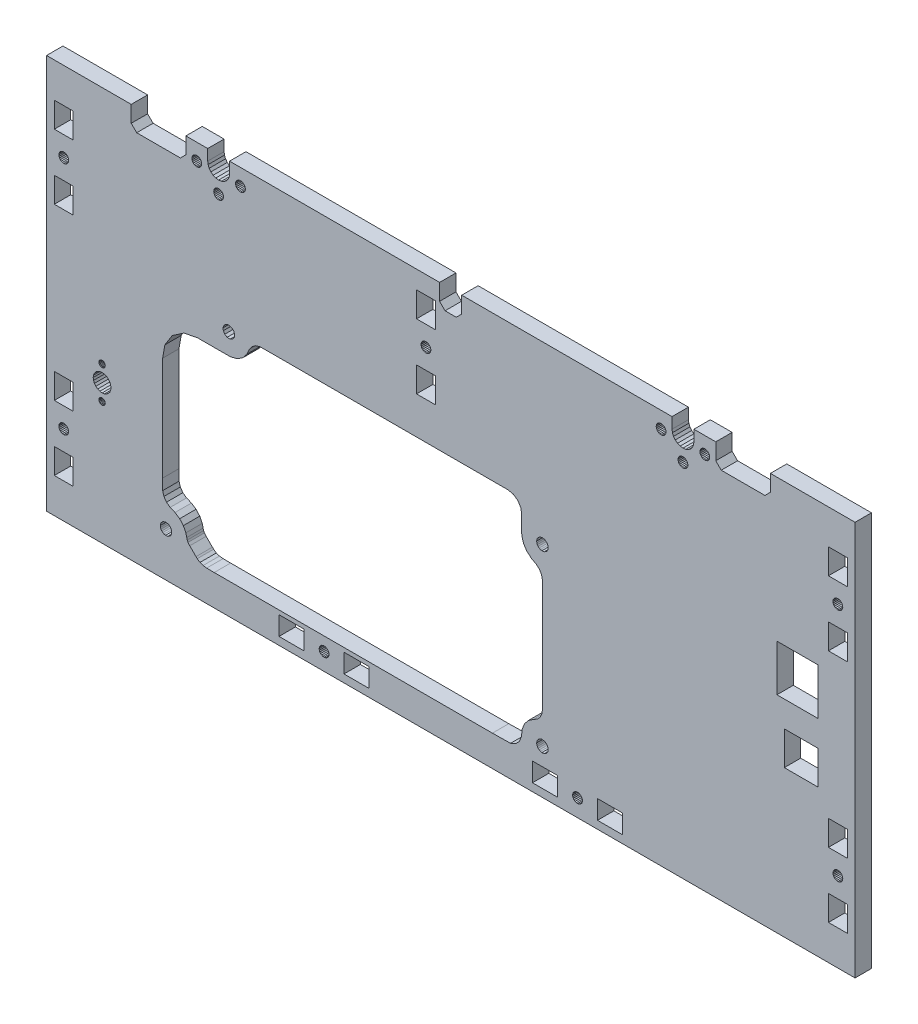
SolidWorks part; units mm, degrees
material "Maple"
ref_plane "Front Plane" through (0, 0, 0) normal (0, 0, 1) x (1, 0, 0)
ref_plane "Top Plane" through (0, 0, 0) normal (0, 1, 0) x (1, 0, 0)
ref_plane "Right Plane" through (0, 0, 0) normal (1, 0, 0) x (0, 0, -1)
sketch "Sketch1" plane through (0, 0, 0) normal (0, 0, 1) x (1, 0, 0)
  line L4690 (-23.9448, -85.7322) -> (-22.9801, -86.1318)
  line L4691 (-201.5036, -85.1681) -> (-201.2176, -85.5408)
  line L4692 (-203.9448, -78.2681) -> (-195.9448, -78.2681)
  line L4693 (-203.9448, -84.2681) -> (-203.9448, -78.2681)
  line L4694 (-187.9448, -78.2681) -> (-111.0448, -78.2681)
  line L4695 (-18.0811, -83.3033) -> (-17.9448, -82.2681)
  line L4696 (-192.98, -86.1318) -> (-191.9448, -86.2681)
  line L4697 (-187.9448, -82.2681) -> (-187.9448, -78.2681)
  line L4698 (10.0552, -78.2681) -> (41.0552, -78.2681)
  line L4699 (8.0552, -86.2681) -> (-7.9448, -86.2681)
  line L4700 (-9.9448, -78.2681) -> (-9.9448, -84.2681)
  line L4701 (-191.9448, -86.2681) -> (-190.9095, -86.1318)
  line L4702 (-25.8085, -83.3033) -> (-25.4089, -84.2681)
  line L4703 (-188.4807, -84.2681) -> (-188.0811, -83.3033)
  line L4704 (-199.0448, -82.7092) -> (-199.4789, -82.5294)
  line L4705 (10.0552, -78.2681) -> (10.0552, -84.2681)
  line L4706 (-200.8448, -85.8269) -> (-200.4106, -86.0067)
  line L4707 (-200.4106, -86.0067) -> (-199.9448, -86.0681)
  line L4708 (-200.4106, -82.5294) -> (-200.8448, -82.7092)
  line L4709 (-198.2061, -83.8022) -> (-198.3859, -83.3681)
  line L4710 (-201.6834, -83.8022) -> (-201.7448, -84.2681)
  line L4711 (41.0552, -78.2681) -> (41.0552, -222.768)
  line L4712 (-201.2176, -82.9953) -> (-201.5036, -83.3681)
  line L4713 (-198.672, -82.9953) -> (-199.0448, -82.7092)
  line L4714 (-199.9448, -82.4681) -> (-200.4106, -82.5294)
  line L4715 (-199.0448, -85.8269) -> (-198.672, -85.5408)
  line L4716 (-198.2061, -84.7339) -> (-198.1448, -84.2681)
  line L4717 (-198.1448, -84.2681) -> (-198.2061, -83.8022)
  line L4718 (-17.9448, -82.2681) -> (-17.9448, -78.2681)
  line L4719 (-198.3859, -83.3681) -> (-198.672, -82.9953)
  line L4720 (-201.5036, -83.3681) -> (-201.6834, -83.8022)
  line L4721 (-25.9448, -82.2681) -> (-25.9448, -78.2681)
  line L4722 (-20.9095, -86.1318) -> (-19.9448, -85.7322)
  line L4723 (-198.672, -85.5408) -> (-198.3859, -85.1681)
  line L4724 (-201.7448, -84.2681) -> (-201.6834, -84.7339)
  line L4725 (-19.1164, -85.0965) -> (-18.4807, -84.2681)
  line L4726 (-198.3859, -85.1681) -> (-198.2061, -84.7339)
  line L4727 (-17.9448, -78.2681) -> (-9.9448, -78.2681)
  line L4728 (-201.2176, -85.5408) -> (-200.8448, -85.8269)
  line L4729 (-189.9448, -85.7322) -> (-189.1163, -85.0965)
  line L4730 (-21.9448, -86.2681) -> (-20.9095, -86.1318)
  line L4731 (-205.9448, -86.2681) -> (-221.9448, -86.2681)
  line L4732 (-203.9448, -84.2681) -> (-205.9448, -86.2681)
  line L4733 (-200.8448, -82.7092) -> (-201.2176, -82.9953)
  line L4734 (-18.4807, -84.2681) -> (-18.0811, -83.3033)
  line L4735 (-19.9448, -85.7322) -> (-19.1164, -85.0965)
  line L4736 (-254.9447, -222.768) -> (-254.9447, -78.2681)
  line L4737 (-22.9801, -86.1318) -> (-21.9448, -86.2681)
  line L4738 (-190.9095, -86.1318) -> (-189.9448, -85.7322)
  line L4739 (-195.4089, -84.2681) -> (-194.7732, -85.0965)
  line L4740 (-254.9447, -78.2681) -> (-223.9448, -78.2681)
  line L4741 (-194.7732, -85.0965) -> (-193.9448, -85.7322)
  line L4742 (-193.9448, -85.7322) -> (-192.98, -86.1318)
  line L4743 (-24.7732, -85.0965) -> (-23.9448, -85.7322)
  line L4744 (41.0552, -222.768) -> (-254.9447, -222.768)
  line L4745 (-25.4089, -84.2681) -> (-24.7732, -85.0965)
  line L4746 (-195.9448, -82.2681) -> (-195.9448, -78.2681)
  line L4747 (-195.8085, -83.3033) -> (-195.4089, -84.2681)
  line L4748 (-188.0811, -83.3033) -> (-187.9448, -82.2681)
  line L4749 (-195.9448, -82.2681) -> (-195.8085, -83.3033)
  line L4750 (-223.9448, -84.2681) -> (-223.9448, -78.2681)
  line L4751 (-223.9448, -84.2681) -> (-221.9448, -86.2681)
  line L4752 (-25.9448, -82.2681) -> (-25.8085, -83.3033)
  line L4753 (-199.4789, -82.5294) -> (-199.9448, -82.4681)
  line L4754 (-189.1163, -85.0965) -> (-188.4807, -84.2681)
  line L4755 (-201.6834, -84.7339) -> (-201.5036, -85.1681)
  line L4756 (10.0552, -84.2681) -> (8.0552, -86.2681)
  line L4757 (-9.9448, -84.2681) -> (-7.9448, -86.2681)
  line L4758 (-199.9448, -86.0681) -> (-199.4789, -86.0067)
  line L4759 (-199.4789, -86.0067) -> (-199.0448, -85.8269)
  line L4760 (35.2215, -105.6777) -> (34.7552, -105.6163)
  line L4761 (35.656, -105.8577) -> (35.2215, -105.6777)
  line L4762 (36.0292, -106.144) -> (35.656, -105.8577)
  line L4763 (36.3155, -106.5172) -> (36.0292, -106.144)
  line L4764 (36.4955, -106.9517) -> (36.3155, -106.5172)
  line L4765 (36.5569, -107.418) -> (36.4955, -106.9517)
  line L4766 (36.4955, -107.8844) -> (36.5569, -107.418)
  line L4767 (36.3155, -108.3189) -> (36.4955, -107.8844)
  line L4768 (36.0292, -108.6921) -> (36.3155, -108.3189)
  line L4769 (35.656, -108.9784) -> (36.0292, -108.6921)
  line L4770 (35.2215, -109.1584) -> (35.656, -108.9784)
  line L4771 (34.7552, -109.2198) -> (35.2215, -109.1584)
  line L4772 (34.2888, -109.1584) -> (34.7552, -109.2198)
  line L4773 (33.8543, -108.9784) -> (34.2888, -109.1584)
  line L4774 (33.4811, -108.6921) -> (33.8543, -108.9784)
  line L4775 (33.1948, -108.3189) -> (33.4811, -108.6921)
  line L4776 (33.0148, -107.8844) -> (33.1948, -108.3189)
  line L4777 (32.9534, -107.418) -> (33.0148, -107.8844)
  line L4778 (33.0148, -106.9517) -> (32.9534, -107.418)
  line L4779 (33.1948, -106.5172) -> (33.0148, -106.9517)
  line L4780 (33.4811, -106.144) -> (33.1948, -106.5172)
  line L4781 (33.8543, -105.8577) -> (33.4811, -106.144)
  line L4782 (34.2888, -105.6777) -> (33.8543, -105.8577)
  line L4783 (34.7552, -105.6163) -> (34.2888, -105.6777)
  line L4784 (-185.5047, -85.1681) -> (-185.2187, -85.5408)
  line L4785 (-185.6846, -84.7339) -> (-185.5047, -85.1681)
  line L4786 (-185.7459, -84.2681) -> (-185.6846, -84.7339)
  line L4787 (-185.6846, -83.8022) -> (-185.7459, -84.2681)
  line L4788 (-185.5047, -83.3681) -> (-185.6846, -83.8022)
  line L4789 (-185.2187, -82.9953) -> (-185.5047, -83.3681)
  line L4790 (-184.8459, -82.7092) -> (-185.2187, -82.9953)
  line L4791 (-184.4118, -82.5294) -> (-184.8459, -82.7092)
  line L4792 (-183.9459, -82.4681) -> (-184.4118, -82.5294)
  line L4793 (-183.48, -82.5294) -> (-183.9459, -82.4681)
  line L4794 (-183.0459, -82.7092) -> (-183.48, -82.5294)
  line L4795 (-182.6731, -82.9953) -> (-183.0459, -82.7092)
  line L4796 (-182.387, -83.3681) -> (-182.6731, -82.9953)
  line L4797 (-182.2072, -83.8022) -> (-182.387, -83.3681)
  line L4798 (-182.1459, -84.2681) -> (-182.2072, -83.8022)
  line L4799 (-182.2072, -84.7339) -> (-182.1459, -84.2681)
  line L4800 (-182.387, -85.1681) -> (-182.2072, -84.7339)
  line L4801 (-182.6731, -85.5408) -> (-182.387, -85.1681)
  line L4802 (-183.0459, -85.8269) -> (-182.6731, -85.5408)
  line L4803 (-183.48, -86.0067) -> (-183.0459, -85.8269)
  line L4804 (-183.9459, -86.0681) -> (-183.48, -86.0067)
  line L4805 (-184.4118, -86.0067) -> (-183.9459, -86.0681)
  line L4806 (-184.8459, -85.8269) -> (-184.4118, -86.0067)
  line L4807 (-185.2187, -85.5408) -> (-184.8459, -85.8269)
  line L4808 (-21.0448, -92.3269) -> (-20.672, -92.0408)
  line L4809 (-21.4789, -92.5067) -> (-21.0448, -92.3269)
  line L4810 (-21.9448, -92.5681) -> (-21.4789, -92.5067)
  line L4811 (-22.4107, -92.5067) -> (-21.9448, -92.5681)
  line L4812 (-22.8448, -92.3269) -> (-22.4107, -92.5067)
  line L4813 (-23.2176, -92.0408) -> (-22.8448, -92.3269)
  line L4814 (-23.5037, -91.6681) -> (-23.2176, -92.0408)
  line L4815 (-23.6835, -91.2339) -> (-23.5037, -91.6681)
  line L4816 (-23.7448, -90.7681) -> (-23.6835, -91.2339)
  line L4817 (-23.6835, -90.3022) -> (-23.7448, -90.7681)
  line L4818 (-23.5037, -89.8681) -> (-23.6835, -90.3022)
  line L4819 (-23.2176, -89.4953) -> (-23.5037, -89.8681)
  line L4820 (-22.8448, -89.2092) -> (-23.2176, -89.4953)
  line L4821 (-22.4107, -89.0294) -> (-22.8448, -89.2092)
  line L4822 (-21.9448, -88.9681) -> (-22.4107, -89.0294)
  line L4823 (-21.4789, -89.0294) -> (-21.9448, -88.9681)
  line L4824 (-21.0448, -89.2092) -> (-21.4789, -89.0294)
  line L4825 (-20.672, -89.4953) -> (-21.0448, -89.2092)
  line L4826 (-20.386, -89.8681) -> (-20.672, -89.4953)
  line L4827 (-20.2062, -90.3022) -> (-20.386, -89.8681)
  line L4828 (-20.1448, -90.7681) -> (-20.2062, -90.3022)
  line L4829 (-20.2062, -91.2339) -> (-20.1448, -90.7681)
  line L4830 (-20.386, -91.6681) -> (-20.2062, -91.2339)
  line L4831 (-20.672, -92.0408) -> (-20.386, -91.6681)
  line L4832 (-15.6846, -83.8022) -> (-15.7459, -84.2681)
  line L4833 (-15.5048, -83.3681) -> (-15.6846, -83.8022)
  line L4834 (-15.2187, -82.9953) -> (-15.5048, -83.3681)
  line L4835 (-14.8459, -82.7092) -> (-15.2187, -82.9953)
  line L4836 (-14.4118, -82.5294) -> (-14.8459, -82.7092)
  line L4837 (-13.9459, -82.4681) -> (-14.4118, -82.5294)
  line L4838 (-13.4801, -82.5294) -> (-13.9459, -82.4681)
  line L4839 (-13.0459, -82.7092) -> (-13.4801, -82.5294)
  line L4840 (-12.6731, -82.9953) -> (-13.0459, -82.7092)
  line L4841 (-12.3871, -83.3681) -> (-12.6731, -82.9953)
  line L4842 (-12.2073, -83.8022) -> (-12.3871, -83.3681)
  line L4843 (-12.1459, -84.2681) -> (-12.2073, -83.8022)
  line L4844 (-12.2073, -84.7339) -> (-12.1459, -84.2681)
  line L4845 (-12.3871, -85.1681) -> (-12.2073, -84.7339)
  line L4846 (-12.6731, -85.5408) -> (-12.3871, -85.1681)
  line L4847 (-13.0459, -85.8269) -> (-12.6731, -85.5408)
  line L4848 (-13.4801, -86.0067) -> (-13.0459, -85.8269)
  line L4849 (-13.9459, -86.0681) -> (-13.4801, -86.0067)
  line L4850 (-14.4118, -86.0067) -> (-13.9459, -86.0681)
  line L4851 (-14.8459, -85.8269) -> (-14.4118, -86.0067)
  line L4852 (-15.2187, -85.5408) -> (-14.8459, -85.8269)
  line L4853 (-15.5048, -85.1681) -> (-15.2187, -85.5408)
  line L4854 (-15.6846, -84.7339) -> (-15.5048, -85.1681)
  line L4855 (-15.7459, -84.2681) -> (-15.6846, -84.7339)
  line L4856 (-250.2051, -108.4189) -> (-249.9188, -108.7921)
  line L4857 (-250.3851, -107.9844) -> (-250.2051, -108.4189)
  line L4858 (-250.4465, -107.518) -> (-250.3851, -107.9844)
  line L4859 (-250.3851, -107.0517) -> (-250.4465, -107.518)
  line L4860 (-250.2051, -106.6172) -> (-250.3851, -107.0517)
  line L4861 (-249.9188, -106.244) -> (-250.2051, -106.6172)
  line L4862 (-249.5456, -105.9577) -> (-249.9188, -106.244)
  line L4863 (-249.1111, -105.7777) -> (-249.5456, -105.9577)
  line L4864 (-248.6447, -105.7163) -> (-249.1111, -105.7777)
  line L4865 (-248.1784, -105.7777) -> (-248.6447, -105.7163)
  line L4866 (-247.7439, -105.9577) -> (-248.1784, -105.7777)
  line L4867 (-247.3707, -106.244) -> (-247.7439, -105.9577)
  line L4868 (-247.0844, -106.6172) -> (-247.3707, -106.244)
  line L4869 (-246.9044, -107.0517) -> (-247.0844, -106.6172)
  line L4870 (-246.843, -107.518) -> (-246.9044, -107.0517)
  line L4871 (-246.9044, -107.9844) -> (-246.843, -107.518)
  line L4872 (-247.0844, -108.4189) -> (-246.9044, -107.9844)
  line L4873 (-247.3707, -108.7921) -> (-247.0844, -108.4189)
  line L4874 (-247.7439, -109.0784) -> (-247.3707, -108.7921)
  line L4875 (-248.1784, -109.2584) -> (-247.7439, -109.0784)
  line L4876 (-248.6447, -109.3198) -> (-248.1784, -109.2584)
  line L4877 (-249.1111, -109.2584) -> (-248.6447, -109.3198)
  line L4878 (-249.5456, -109.0784) -> (-249.1111, -109.2584)
  line L4879 (-249.9188, -108.7921) -> (-249.5456, -109.0784)
  line L4880 (-192.8448, -92.3269) -> (-192.4106, -92.5067)
  line L4881 (-193.2176, -92.0408) -> (-192.8448, -92.3269)
  line L4882 (-193.5036, -91.6681) -> (-193.2176, -92.0408)
  line L4883 (-193.6834, -91.2339) -> (-193.5036, -91.6681)
  line L4884 (-193.7448, -90.7681) -> (-193.6834, -91.2339)
  line L4885 (-193.6834, -90.3022) -> (-193.7448, -90.7681)
  line L4886 (-193.5036, -89.8681) -> (-193.6834, -90.3022)
  line L4887 (-193.2176, -89.4953) -> (-193.5036, -89.8681)
  line L4888 (-192.8448, -89.2092) -> (-193.2176, -89.4953)
  line L4889 (-192.4106, -89.0294) -> (-192.8448, -89.2092)
  line L4890 (-191.9448, -88.9681) -> (-192.4106, -89.0294)
  line L4891 (-191.4789, -89.0294) -> (-191.9448, -88.9681)
  line L4892 (-191.0448, -89.2092) -> (-191.4789, -89.0294)
  line L4893 (-190.672, -89.4953) -> (-191.0448, -89.2092)
  line L4894 (-190.3859, -89.8681) -> (-190.672, -89.4953)
  line L4895 (-190.2061, -90.3022) -> (-190.3859, -89.8681)
  line L4896 (-190.1448, -90.7681) -> (-190.2061, -90.3022)
  line L4897 (-190.2061, -91.2339) -> (-190.1448, -90.7681)
  line L4898 (-190.3859, -91.6681) -> (-190.2061, -91.2339)
  line L4899 (-190.672, -92.0408) -> (-190.3859, -91.6681)
  line L4900 (-191.0448, -92.3269) -> (-190.672, -92.0408)
  line L4901 (-191.4789, -92.5067) -> (-191.0448, -92.3269)
  line L4902 (-191.9448, -92.5681) -> (-191.4789, -92.5067)
  line L4903 (-192.4106, -92.5067) -> (-191.9448, -92.5681)
  line L4904 (-60.5448, -218.2698) -> (-60.0785, -218.2084)
  line L4905 (-61.0111, -218.2084) -> (-60.5448, -218.2698)
  line L4906 (-61.4457, -218.0284) -> (-61.0111, -218.2084)
  line L4907 (-61.8188, -217.7421) -> (-61.4457, -218.0284)
  line L4908 (-62.1052, -217.3689) -> (-61.8188, -217.7421)
  line L4909 (-62.2851, -216.9344) -> (-62.1052, -217.3689)
  line L4910 (-62.3465, -216.468) -> (-62.2851, -216.9344)
  line L4911 (-62.2851, -216.0017) -> (-62.3465, -216.468)
  line L4912 (-62.1052, -215.5672) -> (-62.2851, -216.0017)
  line L4913 (-61.8188, -215.194) -> (-62.1052, -215.5672)
  line L4914 (-61.4457, -214.9077) -> (-61.8188, -215.194)
  line L4915 (-61.0111, -214.7277) -> (-61.4457, -214.9077)
  line L4916 (-60.5448, -214.6663) -> (-61.0111, -214.7277)
  line L4917 (-60.0785, -214.7277) -> (-60.5448, -214.6663)
  line L4918 (-59.644, -214.9077) -> (-60.0785, -214.7277)
  line L4919 (-59.2708, -215.194) -> (-59.644, -214.9077)
  line L4920 (-58.9845, -215.5672) -> (-59.2708, -215.194)
  line L4921 (-58.8045, -216.0017) -> (-58.9845, -215.5672)
  line L4922 (-58.7431, -216.468) -> (-58.8045, -216.0017)
  line L4923 (-58.8045, -216.9344) -> (-58.7431, -216.468)
  line L4924 (-58.9845, -217.3689) -> (-58.8045, -216.9344)
  line L4925 (-59.2708, -217.7421) -> (-58.9845, -217.3689)
  line L4926 (-59.644, -218.0284) -> (-59.2708, -217.7421)
  line L4927 (-60.0785, -218.2084) -> (-59.644, -218.0284)
  line L4928 (-153.8111, -214.7277) -> (-154.2456, -214.9077)
  line L4929 (-153.3448, -214.6663) -> (-153.8111, -214.7277)
  line L4930 (-152.8785, -214.7277) -> (-153.3448, -214.6663)
  line L4931 (-152.4439, -214.9077) -> (-152.8785, -214.7277)
  line L4932 (-152.0708, -215.194) -> (-152.4439, -214.9077)
  line L4933 (-151.7844, -215.5672) -> (-152.0708, -215.194)
  line L4934 (-151.6044, -216.0017) -> (-151.7844, -215.5672)
  line L4935 (-151.5431, -216.468) -> (-151.6044, -216.0017)
  line L4936 (-151.6044, -216.9344) -> (-151.5431, -216.468)
  line L4937 (-151.7844, -217.3689) -> (-151.6044, -216.9344)
  line L4938 (-152.0708, -217.7421) -> (-151.7844, -217.3689)
  line L4939 (-152.4439, -218.0284) -> (-152.0708, -217.7421)
  line L4940 (-152.8785, -218.2084) -> (-152.4439, -218.0284)
  line L4941 (-153.3448, -218.2698) -> (-152.8785, -218.2084)
  line L4942 (-153.8111, -218.2084) -> (-153.3448, -218.2698)
  line L4943 (-154.2456, -218.0284) -> (-153.8111, -218.2084)
  line L4944 (-154.6188, -217.7421) -> (-154.2456, -218.0284)
  line L4945 (-154.9051, -217.3689) -> (-154.6188, -217.7421)
  line L4946 (-155.0851, -216.9344) -> (-154.9051, -217.3689)
  line L4947 (-155.1465, -216.468) -> (-155.0851, -216.9344)
  line L4948 (-155.0851, -216.0017) -> (-155.1465, -216.468)
  line L4949 (-154.9051, -215.5672) -> (-155.0851, -216.0017)
  line L4950 (-154.6188, -215.194) -> (-154.9051, -215.5672)
  line L4951 (-154.2456, -214.9077) -> (-154.6188, -215.194)
  line L4952 (-29.0448, -82.7092) -> (-29.4789, -82.5294)
  line L4953 (-28.672, -82.9953) -> (-29.0448, -82.7092)
  line L4954 (-28.386, -83.3681) -> (-28.672, -82.9953)
  line L4955 (-28.2062, -83.8022) -> (-28.386, -83.3681)
  line L4956 (-28.1448, -84.2681) -> (-28.2062, -83.8022)
  line L4957 (-28.2062, -84.7339) -> (-28.1448, -84.2681)
  line L4958 (-28.386, -85.1681) -> (-28.2062, -84.7339)
  line L4959 (-28.672, -85.5408) -> (-28.386, -85.1681)
  line L4960 (-29.0448, -85.8269) -> (-28.672, -85.5408)
  line L4961 (-29.4789, -86.0067) -> (-29.0448, -85.8269)
  line L4962 (-29.9448, -86.0681) -> (-29.4789, -86.0067)
  line L4963 (-30.4107, -86.0067) -> (-29.9448, -86.0681)
  line L4964 (-30.8448, -85.8269) -> (-30.4107, -86.0067)
  line L4965 (-31.2176, -85.5408) -> (-30.8448, -85.8269)
  line L4966 (-31.5037, -85.1681) -> (-31.2176, -85.5408)
  line L4967 (-31.6835, -84.7339) -> (-31.5037, -85.1681)
  line L4968 (-31.7448, -84.2681) -> (-31.6835, -84.7339)
  line L4969 (-31.6835, -83.8022) -> (-31.7448, -84.2681)
  line L4970 (-31.5037, -83.3681) -> (-31.6835, -83.8022)
  line L4971 (-31.2176, -82.9953) -> (-31.5037, -83.3681)
  line L4972 (-30.8448, -82.7092) -> (-31.2176, -82.9953)
  line L4973 (-30.4107, -82.5294) -> (-30.8448, -82.7092)
  line L4974 (-29.9448, -82.4681) -> (-30.4107, -82.5294)
  line L4975 (-29.4789, -82.5294) -> (-29.9448, -82.4681)
  line L4976 (-44.0448, -213.018) -> (-53.2448, -213.018)
  line L4977 (-44.0448, -219.918) -> (-44.0448, -213.018)
  line L4978 (-53.2448, -219.918) -> (-44.0448, -219.918)
  line L4979 (-53.2448, -213.018) -> (-53.2448, -219.918)
  line L4980 (-77.0448, -213.018) -> (-77.0448, -219.918)
  line L4981 (-67.8448, -213.018) -> (-77.0448, -213.018)
  line L4982 (-67.8448, -219.918) -> (-67.8448, -213.018)
  line L4983 (-77.0448, -219.918) -> (-67.8448, -219.918)
  line L4984 (-169.8448, -213.018) -> (-169.8448, -219.918)
  line L4985 (-160.6448, -213.018) -> (-169.8448, -213.018)
  line L4986 (-160.6448, -219.918) -> (-160.6448, -213.018)
  line L4987 (-169.8448, -219.918) -> (-160.6448, -219.918)
  line L4988 (-146.0448, -213.018) -> (-146.0448, -219.918)
  line L4989 (-136.8448, -213.018) -> (-146.0448, -213.018)
  line L4990 (-136.8448, -219.918) -> (-136.8448, -213.018)
  line L4991 (-146.0448, -219.918) -> (-136.8448, -219.918)
  line L4992 (31.3052, -123.918) -> (38.2052, -123.918)
  line L4993 (31.3052, -114.718) -> (31.3052, -123.918)
  line L4994 (38.2052, -114.718) -> (31.3052, -114.718)
  line L4995 (38.2052, -123.918) -> (38.2052, -114.718)
  line L4996 (31.3052, -100.118) -> (38.2052, -100.118)
  line L4997 (31.3052, -90.9181) -> (31.3052, -100.118)
  line L4998 (38.2052, -90.9181) -> (31.3052, -90.9181)
  line L4999 (38.2052, -100.118) -> (38.2052, -90.9181)
  line L5000 (-245.1947, -124.018) -> (-245.1947, -114.818)
  line L5001 (-252.0947, -124.018) -> (-245.1947, -124.018)
  line L5002 (-252.0947, -114.818) -> (-252.0947, -124.018)
  line L5003 (-245.1947, -114.818) -> (-252.0947, -114.818)
  line L5004 (-245.1947, -100.218) -> (-245.1947, -91.0181)
  line L5005 (-252.0947, -100.218) -> (-245.1947, -100.218)
  line L5006 (-252.0947, -91.0181) -> (-252.0947, -100.218)
  line L5007 (-245.1947, -91.0181) -> (-252.0947, -91.0181)
  line L5008 (-245.1947, -200.818) -> (-252.0947, -200.818)
  line L5009 (-252.0947, -177.018) -> (-252.0947, -186.218)
  line L5010 (-246.9044, -193.9844) -> (-246.843, -193.518)
  line L5011 (-249.1111, -195.2584) -> (-248.6447, -195.3198)
  line L5012 (-247.3707, -192.244) -> (-247.7439, -191.9577)
  line L5013 (-248.1784, -195.2584) -> (-247.7439, -195.0784)
  line L5014 (-250.4465, -193.518) -> (-250.3851, -193.9844)
  line L5015 (-245.1947, -210.018) -> (-245.1947, -200.818)
  line L5016 (-250.2051, -194.4189) -> (-249.9188, -194.7921)
  line L5017 (-248.6447, -195.3198) -> (-248.1784, -195.2584)
  line L5018 (-247.7439, -191.9577) -> (-248.1784, -191.7777)
  line L5019 (-252.0947, -186.218) -> (-245.1947, -186.218)
  line L5020 (-248.1784, -191.7777) -> (-248.6447, -191.7163)
  line L5021 (-247.7439, -195.0784) -> (-247.3707, -194.7921)
  line L5022 (-249.5456, -195.0784) -> (-249.1111, -195.2584)
  line L5023 (-252.0947, -210.018) -> (-245.1947, -210.018)
  line L5024 (-247.0844, -194.4189) -> (-246.9044, -193.9844)
  line L5025 (-246.9044, -193.0517) -> (-247.0844, -192.6172)
  line L5026 (-246.843, -193.518) -> (-246.9044, -193.0517)
  line L5027 (-250.2051, -192.6172) -> (-250.3851, -193.0517)
  line L5028 (-249.1111, -191.7777) -> (-249.5456, -191.9577)
  line L5029 (-250.3851, -193.9844) -> (-250.2051, -194.4189)
  line L5030 (-252.0947, -200.818) -> (-252.0947, -210.018)
  line L5031 (-250.3851, -193.0517) -> (-250.4465, -193.518)
  line L5032 (-247.3707, -194.7921) -> (-247.0844, -194.4189)
  line L5033 (-249.9188, -194.7921) -> (-249.5456, -195.0784)
  line L5034 (-245.1947, -177.018) -> (-252.0947, -177.018)
  line L5035 (-245.1947, -186.218) -> (-245.1947, -177.018)
  line L5036 (-247.0844, -192.6172) -> (-247.3707, -192.244)
  line L5037 (-249.5456, -191.9577) -> (-249.9188, -192.244)
  line L5038 (-249.9188, -192.244) -> (-250.2051, -192.6172)
  line L5039 (-248.6447, -191.7163) -> (-249.1111, -191.7777)
  line L5040 (31.3052, -210.018) -> (38.2052, -210.018)
  line L5041 (36.4955, -193.9844) -> (36.5569, -193.518)
  line L5042 (38.2052, -177.018) -> (31.3052, -177.018)
  line L5043 (33.1948, -192.6172) -> (33.0148, -193.0517)
  line L5044 (33.0148, -193.9844) -> (33.1948, -194.4189)
  line L5045 (33.4811, -194.7921) -> (33.8543, -195.0784)
  line L5046 (33.0148, -193.0517) -> (32.9534, -193.518)
  line L5047 (34.2888, -191.7777) -> (33.8543, -191.9577)
  line L5048 (33.1948, -194.4189) -> (33.4811, -194.7921)
  line L5049 (34.7552, -191.7163) -> (34.2888, -191.7777)
  line L5050 (35.2215, -191.7777) -> (34.7552, -191.7163)
  line L5051 (32.9534, -193.518) -> (33.0148, -193.9844)
  line L5052 (33.8543, -191.9577) -> (33.4811, -192.244)
  line L5053 (36.0292, -192.244) -> (35.656, -191.9577)
  line L5054 (34.7552, -195.3198) -> (35.2215, -195.2584)
  line L5055 (33.8543, -195.0784) -> (34.2888, -195.2584)
  line L5056 (38.2052, -186.218) -> (38.2052, -177.018)
  line L5057 (35.656, -195.0784) -> (36.0292, -194.7921)
  line L5058 (36.3155, -194.4189) -> (36.4955, -193.9844)
  line L5059 (36.5569, -193.518) -> (36.4955, -193.0517)
  line L5060 (31.3052, -177.018) -> (31.3052, -186.218)
  line L5061 (36.0292, -194.7921) -> (36.3155, -194.4189)
  line L5062 (31.3052, -186.218) -> (38.2052, -186.218)
  line L5063 (35.2215, -195.2584) -> (35.656, -195.0784)
  line L5064 (36.3155, -192.6172) -> (36.0292, -192.244)
  line L5065 (38.2052, -210.018) -> (38.2052, -200.818)
  line L5066 (36.4955, -193.0517) -> (36.3155, -192.6172)
  line L5067 (33.4811, -192.244) -> (33.1948, -192.6172)
  line L5068 (34.2888, -195.2584) -> (34.7552, -195.3198)
  line L5069 (35.656, -191.9577) -> (35.2215, -191.7777)
  line L5070 (31.3052, -200.818) -> (31.3052, -210.018)
  line L5071 (38.2052, -200.818) -> (31.3052, -200.818)
  line L5072 (-232.9939, -174.6697) -> (-232.3209, -174.1532)
  line L5073 (-235.7539, -166.1902) -> (-235.6365, -166.4736)
  line L5074 (-234.6189, -164.7111) -> (-234.9231, -164.7511)
  line L5075 (-234.3148, -178.9591) -> (-234.0314, -178.8417)
  line L5076 (-234.9231, -164.7511) -> (-235.2064, -164.8685)
  line L5077 (-236.917, -169.557) -> (-237.4335, -170.2301)
  line L5078 (-232.3209, -169.557) -> (-232.9939, -169.0405)
  line L5079 (-235.2064, -166.9037) -> (-234.9231, -167.0211)
  line L5080 (-234.6189, -176.6491) -> (-234.9231, -176.6891)
  line L5081 (-233.7881, -176.9933) -> (-234.0314, -176.8065)
  line L5082 (-235.7539, -177.52) -> (-235.7939, -177.8241)
  line L5083 (-233.7881, -165.0553) -> (-234.0314, -164.8685)
  line L5084 (-231.4797, -172.6963) -> (-231.3689, -171.8551)
  line L5085 (-237.4335, -170.2301) -> (-237.7582, -171.0139)
  line L5086 (-233.484, -166.1902) -> (-233.4439, -165.8861)
  line L5087 (-233.7778, -168.7159) -> (-234.6189, -168.6051)
  line L5088 (-233.7778, -174.9944) -> (-232.9939, -174.6697)
  line L5089 (-235.4601, -168.7159) -> (-236.2439, -169.0405)
  line L5090 (-234.6189, -178.9991) -> (-234.3148, -178.9591)
  line L5091 (-233.6014, -178.4116) -> (-233.484, -178.1282)
  line L5092 (-235.4498, -176.9933) -> (-235.6365, -177.2366)
  line L5093 (-234.3148, -167.0211) -> (-234.0314, -166.9037)
  line L5094 (-232.9939, -169.0405) -> (-233.7778, -168.7159)
  line L5095 (-235.2064, -178.8417) -> (-234.9231, -178.9591)
  line L5096 (-237.7582, -172.6963) -> (-237.4335, -173.4801)
  line L5097 (-233.7881, -166.717) -> (-233.6014, -166.4736)
  line L5098 (-234.6189, -168.6051) -> (-235.4601, -168.7159)
  line L5099 (-236.2439, -169.0405) -> (-236.917, -169.557)
  line L5100 (-235.2064, -176.8065) -> (-235.4498, -176.9933)
  line L5101 (-234.0314, -176.8065) -> (-234.3148, -176.6891)
  line L5102 (-234.0314, -166.9037) -> (-233.7881, -166.717)
  line L5103 (-235.6365, -178.4116) -> (-235.4498, -178.655)
  line L5104 (-233.6014, -177.2366) -> (-233.7881, -176.9933)
  line L5105 (-236.917, -174.1532) -> (-236.2439, -174.6697)
  line L5106 (-232.3209, -174.1532) -> (-231.8044, -173.4801)
  line L5107 (-231.3689, -171.8551) -> (-231.4797, -171.0139)
  line L5108 (-235.4601, -174.9944) -> (-234.6189, -175.1051)
  line L5109 (-234.6189, -175.1051) -> (-233.7778, -174.9944)
  line L5110 (-235.7539, -165.582) -> (-235.7939, -165.8861)
  line L5111 (-233.484, -178.1282) -> (-233.4439, -177.8241)
  line L5112 (-233.4439, -165.8861) -> (-233.484, -165.582)
  line L5113 (-235.6365, -166.4736) -> (-235.4498, -166.717)
  line L5114 (-234.0314, -164.8685) -> (-234.3148, -164.7511)
  line L5115 (-237.8689, -171.8551) -> (-237.7582, -172.6963)
  line L5116 (-233.7881, -178.655) -> (-233.6014, -178.4116)
  line L5117 (-233.6014, -166.4736) -> (-233.484, -166.1902)
  line L5118 (-231.8044, -170.2301) -> (-232.3209, -169.557)
  line L5119 (-233.484, -165.582) -> (-233.6014, -165.2986)
  line L5120 (-235.7939, -165.8861) -> (-235.7539, -166.1902)
  line L5121 (-235.6365, -177.2366) -> (-235.7539, -177.52)
  line L5122 (-235.2064, -164.8685) -> (-235.4498, -165.0553)
  line L5123 (-235.4498, -178.655) -> (-235.2064, -178.8417)
  line L5124 (-234.3148, -164.7511) -> (-234.6189, -164.7111)
  line L5125 (-235.7539, -178.1282) -> (-235.6365, -178.4116)
  line L5126 (-235.4498, -166.717) -> (-235.2064, -166.9037)
  line L5127 (-234.9231, -176.6891) -> (-235.2064, -176.8065)
  line L5128 (-237.7582, -171.0139) -> (-237.8689, -171.8551)
  line L5129 (-231.4797, -171.0139) -> (-231.8044, -170.2301)
  line L5130 (-231.8044, -173.4801) -> (-231.4797, -172.6963)
  line L5131 (-234.6189, -167.0611) -> (-234.3148, -167.0211)
  line L5132 (-233.484, -177.52) -> (-233.6014, -177.2366)
  line L5133 (-233.6014, -165.2986) -> (-233.7881, -165.0553)
  line L5134 (-234.0314, -178.8417) -> (-233.7881, -178.655)
  line L5135 (-233.4439, -177.8241) -> (-233.484, -177.52)
  line L5136 (-237.4335, -173.4801) -> (-236.917, -174.1532)
  line L5137 (-236.2439, -174.6697) -> (-235.4601, -174.9944)
  line L5138 (-235.7939, -177.8241) -> (-235.7539, -178.1282)
  line L5139 (-234.9231, -178.9591) -> (-234.6189, -178.9991)
  line L5140 (-234.3148, -176.6891) -> (-234.6189, -176.6491)
  line L5141 (-235.4498, -165.0553) -> (-235.6365, -165.2986)
  line L5142 (-235.6365, -165.2986) -> (-235.7539, -165.582)
  line L5143 (-234.9231, -167.0211) -> (-234.6189, -167.0611)
  line L5144 (-114.3045, -100.8808) -> (-114.4845, -100.4463)
  line L5145 (-119.4948, -94.0471) -> (-112.5948, -94.0471)
  line L5146 (-119.4948, -108.6471) -> (-119.4948, -117.8471)
  line L5147 (-115.5785, -103.0875) -> (-115.1439, -102.9075)
  line L5148 (-117.3188, -102.6211) -> (-116.9457, -102.9075)
  line L5149 (-119.4948, -84.8471) -> (-119.4948, -94.0471)
  line L5150 (-119.4948, -117.8471) -> (-112.5948, -117.8471)
  line L5151 (-112.5948, -108.6471) -> (-119.4948, -108.6471)
  line L5152 (-116.5111, -103.0875) -> (-116.0448, -103.1488)
  line L5153 (-112.5948, -94.0471) -> (-112.5948, -84.8471)
  line L5154 (-117.7851, -100.8808) -> (-117.8465, -101.3471)
  line L5155 (-114.7708, -100.0731) -> (-115.1439, -99.7868)
  line L5156 (-116.5111, -99.6068) -> (-116.9457, -99.7868)
  line L5157 (-117.6051, -102.248) -> (-117.3188, -102.6211)
  line L5158 (-117.3188, -100.0731) -> (-117.6051, -100.4463)
  line L5159 (-116.0448, -99.5454) -> (-116.5111, -99.6068)
  line L5160 (-114.4845, -100.4463) -> (-114.7708, -100.0731)
  line L5161 (-112.5948, -117.8471) -> (-112.5948, -108.6471)
  line L5162 (-114.7708, -102.6211) -> (-114.4845, -102.248)
  line L5163 (-116.9457, -102.9075) -> (-116.5111, -103.0875)
  line L5164 (-116.9457, -99.7868) -> (-117.3188, -100.0731)
  line L5165 (-117.6051, -100.4463) -> (-117.7851, -100.8808)
  line L5166 (-114.2431, -101.3471) -> (-114.3045, -100.8808)
  line L5167 (-116.0448, -103.1488) -> (-115.5785, -103.0875)
  line L5168 (-114.3045, -101.8134) -> (-114.2431, -101.3471)
  line L5169 (-117.7851, -101.8134) -> (-117.6051, -102.248)
  line L5170 (-112.5948, -84.8471) -> (-119.4948, -84.8471)
  line L5171 (-117.8465, -101.3471) -> (-117.7851, -101.8134)
  line L5172 (-114.4845, -102.248) -> (-114.3045, -101.8134)
  line L5173 (-115.5785, -99.6068) -> (-116.0448, -99.5454)
  line L5174 (-115.1439, -102.9075) -> (-114.7708, -102.6211)
  line L5175 (-115.1439, -99.7868) -> (-115.5785, -99.6068)
  line L5176 (-102.9448, -84.2681) -> (-104.9448, -86.2681)
  line L5177 (-111.0448, -84.2681) -> (-111.0448, -78.2681)
  line L5178 (-111.0448, -84.2681) -> (-109.0448, -86.2681)
  line L5179 (-102.9448, -84.2681) -> (-102.9448, -78.2681)
  line L5180 (-104.9448, -86.2681) -> (-109.0448, -86.2681)
  line L5181 (-102.9448, -78.2681) -> (-25.9448, -78.2681)
  line L5182 (12.4552, -147.268) -> (27.4552, -147.268)
  line L5183 (27.4552, -147.268) -> (27.4552, -130.268)
  line L5184 (27.4552, -130.268) -> (12.4552, -130.268)
  line L5185 (12.4552, -130.268) -> (12.4552, -147.268)
  line L5186 (-213.0593, -205.5053) -> (-212.3789, -204.7562)
  line L5187 (-213.3158, -206.5182) -> (-213.0593, -205.5053)
  line L5188 (-213.2489, -207.0493) -> (-213.3158, -206.5182)
  line L5189 (-213.0593, -207.5311) -> (-213.2489, -207.0493)
  line L5190 (-212.7637, -207.947) -> (-213.0593, -207.5311)
  line L5191 (-212.3789, -208.2803) -> (-212.7637, -207.947)
  line L5192 (-211.9214, -208.5143) -> (-212.3789, -208.2803)
  line L5193 (-211.408, -208.6323) -> (-211.9214, -208.5143)
  line L5194 (-210.5588, -208.5477) -> (-211.408, -208.6323)
  line L5195 (-209.6882, -208.0208) -> (-210.5588, -208.5477)
  line L5196 (-209.1613, -207.1501) -> (-209.6882, -208.0208)
  line L5197 (-209.1089, -206.09) -> (-209.1613, -207.1501)
  line L5198 (-209.551, -205.1665) -> (-209.1089, -206.09)
  line L5199 (-210.3636, -204.5602) -> (-209.551, -205.1665)
  line L5200 (-211.408, -204.4042) -> (-210.3636, -204.5602)
  line L5201 (-212.3789, -204.7562) -> (-211.408, -204.4042)
  line L5202 (-77.3063, -149.0478) -> (-75.6319, -149.9354)
  line L5203 (-196.319, -211.4877) -> (-197.6194, -211.3108)
  line L5204 (-197.6194, -211.3108) -> (-198.781, -210.9176)
  line L5205 (-198.781, -210.9176) -> (-199.7729, -210.242)
  line L5206 (-199.7729, -210.242) -> (-200.2238, -209.7965)
  line L5207 (-188.8307, -134.5655) -> (-189.7014, -134.0386)
  line L5208 (-183.0844, -138.1721) -> (-181.5574, -136.2599)
  line L5209 (-181.5574, -136.2599) -> (-180.6953, -134.2876)
  line L5210 (-180.6953, -134.2876) -> (-179.7281, -132.9533)
  line L5211 (-179.7281, -132.9533) -> (-178.4065, -132.0216)
  line L5212 (-178.4065, -132.0216) -> (-176.8219, -131.5579)
  line L5213 (-206.2045, -200.7679) -> (-207.9071, -199.6465)
  line L5214 (-207.9071, -199.6465) -> (-209.6831, -198.9373)
  line L5215 (-209.6831, -198.9373) -> (-211.0372, -197.9553)
  line L5216 (-211.0372, -197.9553) -> (-211.9777, -196.606)
  line L5217 (-211.9777, -196.606) -> (-212.4332, -194.9865)
  line L5218 (-74.5789, -208.2803) -> (-74.9637, -207.947)
  line L5219 (-74.9637, -207.947) -> (-75.2593, -207.5311)
  line L5220 (-84.0261, -131.9578) -> (-82.3663, -133.1494)
  line L5221 (-71.3089, -206.09) -> (-71.3613, -207.1501)
  line L5222 (-71.3613, -207.1501) -> (-71.8882, -208.0208)
  line L5223 (-71.8882, -208.0208) -> (-72.7588, -208.5477)
  line L5224 (-72.7588, -208.5477) -> (-73.608, -208.6323)
  line L5225 (-73.608, -208.6323) -> (-74.1214, -208.5143)
  line L5226 (-80.004, -202.744) -> (-80.8349, -204.8912)
  line L5227 (-80.8349, -204.8912) -> (-81.066, -207.1881)
  line L5228 (-75.2726, -198.8406) -> (-76.7281, -199.6725)
  line L5229 (-76.7281, -199.6725) -> (-78.5961, -200.9656)
  line L5230 (-85.0728, -211.4154) -> (-91.718, -211.518)
  line L5231 (-193.5709, -211.518) -> (-196.319, -211.4877)
  line L5232 (-75.6319, -149.9354) -> (-74.4991, -150.959)
  line L5233 (-74.4991, -150.959) -> (-73.7416, -152.2605)
  line L5234 (-73.7416, -152.2605) -> (-73.4043, -153.7711)
  line L5235 (-73.4043, -153.7711) -> (-73.391, -158.3897)
  line L5236 (-204.8593, -202.2915) -> (-206.2045, -200.7679)
  line L5237 (-186.2407, -133.3632) -> (-186.8471, -134.1758)
  line L5238 (-186.8471, -134.1758) -> (-187.7705, -134.6179)
  line L5239 (-189.7014, -134.0386) -> (-190.2282, -133.1679)
  line L5240 (-190.2282, -133.1679) -> (-190.3128, -132.3188)
  line L5241 (-190.3128, -132.3188) -> (-190.1948, -131.8054)
  line L5242 (-74.5789, -144.2803) -> (-74.9637, -143.947)
  line L5243 (-74.9637, -143.947) -> (-75.2593, -143.5311)
  line L5244 (-75.2593, -143.5311) -> (-75.4489, -143.0493)
  line L5245 (-75.4489, -143.0493) -> (-75.5158, -142.5182)
  line L5246 (-186.4367, -131.3479) -> (-186.0847, -132.3188)
  line L5247 (-72.5636, -204.5602) -> (-71.751, -205.1665)
  line L5248 (-71.751, -205.1665) -> (-71.3089, -206.09)
  line L5249 (-81.011, -142.0999) -> (-80.9553, -143.438)
  line L5250 (-80.9553, -143.438) -> (-80.3175, -145.6849)
  line L5251 (-80.3175, -145.6849) -> (-79.0617, -147.5943)
  line L5252 (-79.0617, -147.5943) -> (-77.3063, -149.0478)
  line L5253 (-187.7705, -134.6179) -> (-188.8307, -134.5655)
  line L5254 (-74.1214, -144.5143) -> (-74.5789, -144.2803)
  line L5255 (-188.1988, -130.411) -> (-187.1859, -130.6675)
  line L5256 (-187.1859, -130.6675) -> (-186.4367, -131.3479)
  line L5257 (-75.5158, -206.5182) -> (-75.2593, -205.5053)
  line L5258 (-75.2593, -205.5053) -> (-74.5789, -204.7562)
  line L5259 (-202.5162, -207.5176) -> (-203.1563, -206.7803)
  line L5260 (-203.1563, -206.7803) -> (-203.453, -206.1796)
  line L5261 (-203.453, -206.1796) -> (-203.6241, -205.451)
  line L5262 (-203.6241, -205.451) -> (-203.9555, -204.133)
  line L5263 (-203.9555, -204.133) -> (-204.8593, -202.2915)
  line L5264 (-186.0847, -132.3188) -> (-186.2407, -133.3632)
  line L5265 (-188.7298, -130.4779) -> (-188.1988, -130.411)
  line L5266 (-189.2117, -130.6675) -> (-188.7298, -130.4779)
  line L5267 (-189.6276, -130.9631) -> (-189.2117, -130.6675)
  line L5268 (-189.9608, -131.3479) -> (-189.6276, -130.9631)
  line L5269 (-190.1948, -131.8054) -> (-189.9608, -131.3479)
  line L5270 (-74.1214, -208.5143) -> (-74.5789, -208.2803)
  line L5271 (-73.608, -204.4042) -> (-72.5636, -204.5602)
  line L5272 (-74.5789, -204.7562) -> (-73.608, -204.4042)
  line L5273 (-75.4489, -207.0493) -> (-75.5158, -206.5182)
  line L5274 (-75.2593, -207.5311) -> (-75.4489, -207.0493)
  line L5275 (-73.608, -144.6323) -> (-74.1214, -144.5143)
  line L5276 (-72.7588, -144.5477) -> (-73.608, -144.6323)
  line L5277 (-71.8882, -144.0208) -> (-72.7588, -144.5477)
  line L5278 (-71.3613, -143.1501) -> (-71.8882, -144.0208)
  line L5279 (-71.3089, -142.09) -> (-71.3613, -143.1501)
  line L5280 (-71.751, -141.1665) -> (-71.3089, -142.09)
  line L5281 (-72.5636, -140.5602) -> (-71.751, -141.1665)
  line L5282 (-73.608, -140.4042) -> (-72.5636, -140.5602)
  line L5283 (-74.5789, -140.7562) -> (-73.608, -140.4042)
  line L5284 (-75.2593, -141.5053) -> (-74.5789, -140.7562)
  line L5285 (-75.5158, -142.5182) -> (-75.2593, -141.5053)
  line L5286 (-176.8219, -131.5579) -> (-174.4807, -131.518)
  line L5287 (-82.3663, -133.1494) -> (-81.3031, -134.9012)
  line L5288 (-81.3031, -134.9012) -> (-81.011, -136.641)
  line L5289 (-212.4332, -194.9865) -> (-212.465, -191.0316)
  line L5290 (-212.465, -153.0267) -> (-211.6488, -148.3805)
  line L5291 (-211.6488, -148.3805) -> (-208.9089, -144.0569)
  line L5292 (-208.9089, -144.0569) -> (-204.7003, -141.1566)
  line L5293 (-204.7003, -141.1566) -> (-199.7596, -140.1558)
  line L5294 (-78.5961, -200.9656) -> (-80.004, -202.744)
  line L5295 (-86.091, -131.518) -> (-84.0261, -131.9578)
  line L5296 (-81.066, -207.1881) -> (-81.784, -209.1284)
  line L5297 (-81.784, -209.1284) -> (-83.1828, -210.6003)
  line L5298 (-83.1828, -210.6003) -> (-85.0728, -211.4154)
  line L5299 (-73.391, -194.8631) -> (-73.6004, -196.3623)
  line L5300 (-73.6004, -196.3623) -> (-74.2424, -197.7306)
  line L5301 (-74.2424, -197.7306) -> (-75.2726, -198.8406)
  line L5302 (-189.4018, -140.1558) -> (-187.5783, -140.1306)
  line L5303 (-187.5783, -140.1306) -> (-185.1403, -139.5113)
  line L5304 (-185.1403, -139.5113) -> (-183.0844, -138.1721)
  line L8409 (-202.5162, -207.5176) -> (-200.2238, -209.7965)
  line L8410 (-189.4018, -140.1558) -> (-199.7596, -140.1558)
  line L8411 (-193.5709, -211.518) -> (-91.718, -211.518)
  line L8412 (-86.091, -131.518) -> (-174.4807, -131.518)
  line L8413 (-81.011, -142.0999) -> (-81.011, -136.641)
  line L8414 (-73.391, -194.8631) -> (-73.391, -158.3897)
  line L8415 (-212.465, -153.0267) -> (-212.465, -191.0316)
  line L9294 (-118.1119, -218.5237) -> (-118.1119, -214.2158)
  line L9295 (-118.1119, -214.2158) -> (-115.9827, -214.2158)
  line L9296 (-115.9827, -214.2158) -> (-118.1119, -214.2158)
  line L9297 (-118.1119, -214.2158) -> (-118.1119, -216.3073)
  line L9298 (-118.1119, -216.3073) -> (-116.2824, -216.3073)
  line L9299 (-116.2824, -216.3073) -> (-118.1119, -216.3073)
  line L9300 (-118.1119, -216.3073) -> (-118.1119, -218.5237)
  line L9301 (-118.1119, -218.5237) -> (-115.9827, -218.5237)
  line L9302 (-115.9827, -218.5237) -> (-118.1119, -218.5237)
  line L9980 (15.1552, -169.0169) -> (27.4552, -169.0169)
  line L9981 (27.4552, -169.0169) -> (27.4552, -156.7169)
  line L9982 (27.4552, -156.7169) -> (15.1552, -156.7169)
  line L9983 (15.1552, -156.7169) -> (15.1552, -169.0169)
extrude "Boss-Extrude1" add sketch "Sketch1" along normal blind 6
